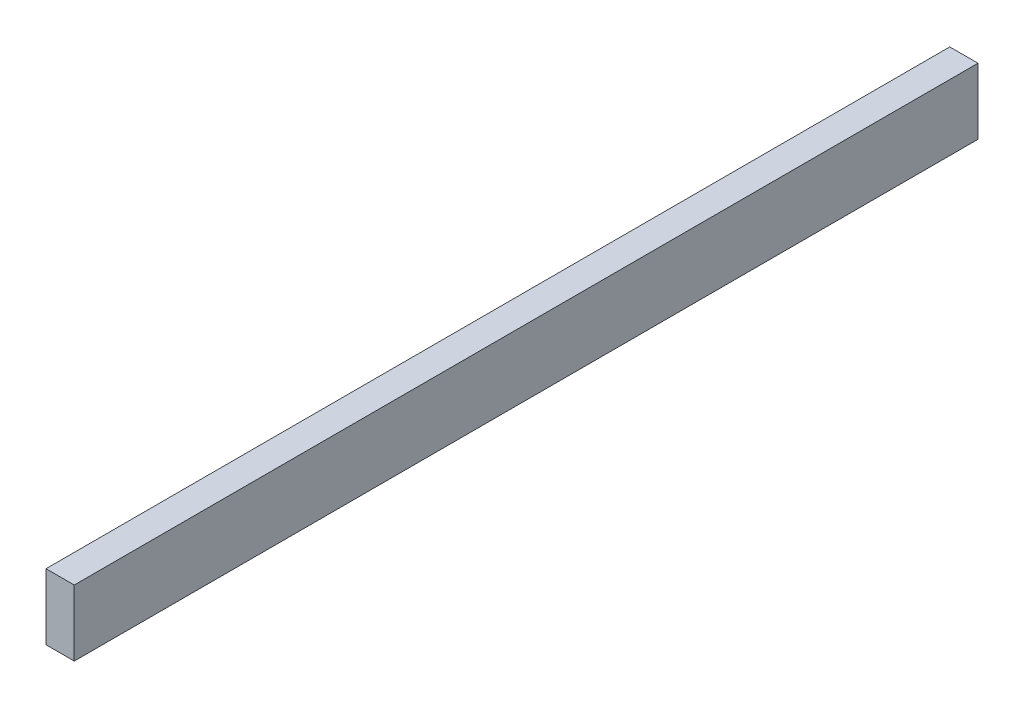
SolidWorks part; units mm, degrees
material "Pine"
ref_plane "Front Plane" through (0, 0, 0) normal (0, 0, 1) x (1, 0, 0)
ref_plane "Top Plane" through (0, 0, 0) normal (0, 1, 0) x (1, 0, 0)
ref_plane "Right Plane" through (0, 0, 0) normal (1, 0, 0) x (0, 0, -1)
sketch "Sketch1" plane through (0, 0, 0) normal (0, 0, 1) x (1, 0, 0)
  line L1 (-38.1, 51.2664) -> (0, 51.2664)
  line L2 (-38.1, 51.2664) -> (-38.1, -37.6336)
  line L3 (-38.1, -37.6336) -> (0, -37.6336)
  line L4 (0, 51.2664) -> (0, -37.6336)
  dimension "D1" = 88.9
  dimension "D2" = 38.1
extrude "Boss-Extrude1" add sketch "Sketch1" along normal blind 1219.2
